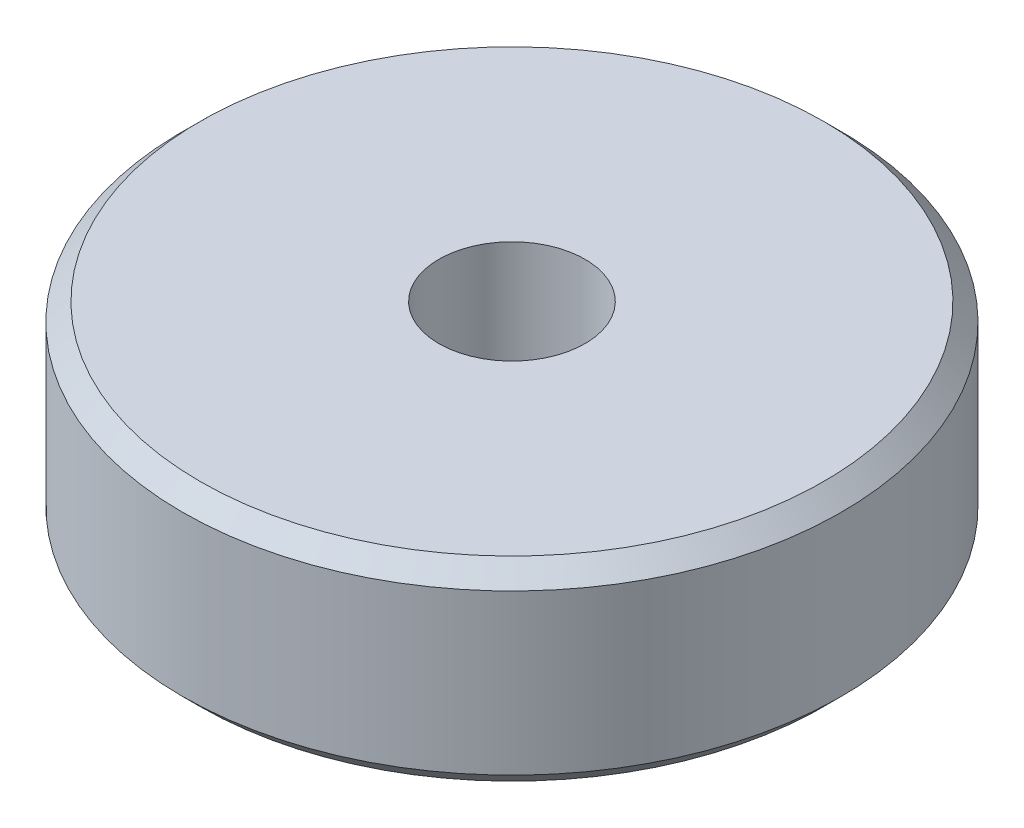
SolidWorks part; units mm, degrees
material "ABS"
ref_plane "Front" through (0, 0, 0) normal (0, 0, 1) x (1, 0, 0)
ref_plane "Top" through (0, 0, 0) normal (0, 1, 0) x (1, 0, 0)
ref_plane "Right" through (0, 0, 0) normal (1, 0, 0) x (0, 0, -1)
sketch "Sketch1" plane through (0, 0, 0) normal (0, 1, 0) x (1, 0, 0)
  circle A0 centre (0, 0) radius 18.595
  dimension "D1" = 37.19
extrude "Boss-Extrude1" add sketch "Sketch1" along normal blind 11
sketch "Sketch2" plane through (0, 11, 0) normal (0, 1, 0) x (1, 0, 0)
  circle A0 centre (0, 0) radius 4.125
  dimension "D1" = 8.25
extrude "Cut-Extrude1" cut sketch "Sketch2" against normal through all contours A0
chamfer "Chamfer1" distance 1 angle 45 2 edges at (0, 0, 18.595) (0, 11, 18.595)
